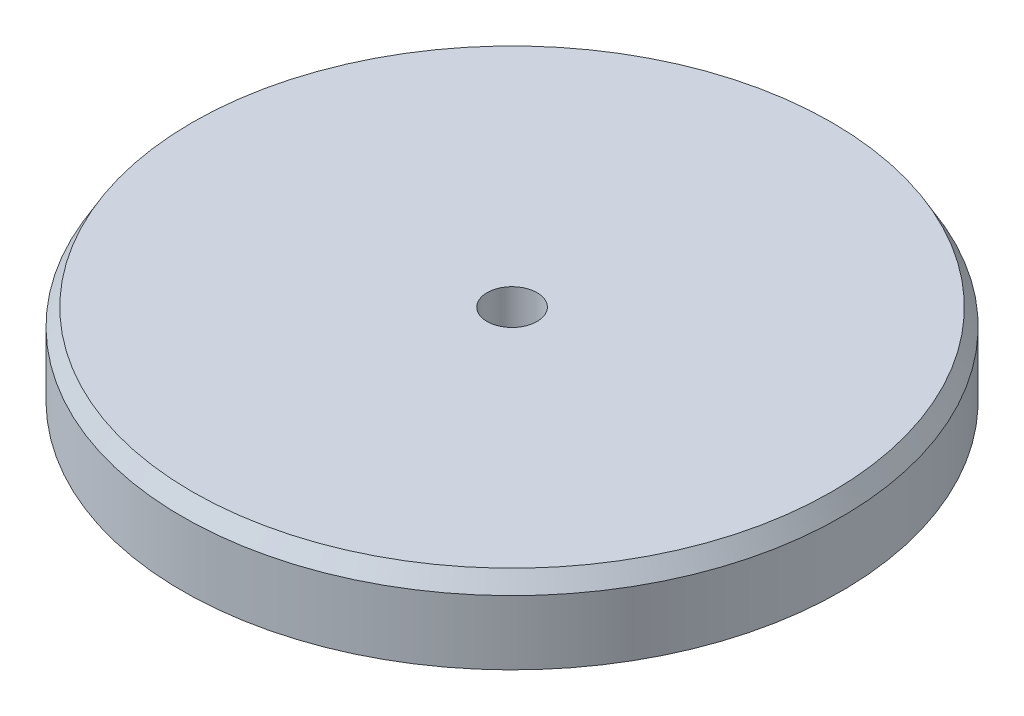
SolidWorks part; units mm, degrees
ref_plane "Front Plane" through (0, 0, 0) normal (0, 0, 1) x (1, 0, 0)
ref_plane "Top Plane" through (0, 0, 0) normal (0, 1, 0) x (1, 0, 0)
ref_plane "Right Plane" through (0, 0, 0) normal (1, 0, 0) x (0, 0, -1)
sketch "Sketch1" plane through (0, 0, 0) normal (1, 0, 0) x (0, 0, -1)
  line L0 (0, 0) -> (0, 10.2967) construction
  line L1 (-0.9779, 0) -> (-0.9779, 7.62)
  line L2 (-0.9779, 7.62) -> (-12.8905, 7.62)
  line L3 (-12.8905, 7.62) -> (-12.8905, 4.445)
  line L4 (-12.8905, 4.445) -> (-7.62, 4.445)
  line L5 (-5.08, 1.905) -> (-5.08, 0)
  line L6 (-5.08, 0) -> (-0.9779, 0)
  arc A0 (-7.62, 4.445) -> (-5.08, 1.905) centre (-7.62, 1.905) cw
  dimension "D6" = 2.54
  dimension "D1" = 1.9558
  dimension "D2" = 7.62
  dimension "D3" = 3.175
  dimension "D4" = 25.781
  dimension "D5" = 10.16
revolve "Revolve1" add sketch "Sketch1" angle 360 about L0
chamfer "Chamfer1" distance 0.381 angle 60 1 edges at (0, 7.62, -12.8905)
